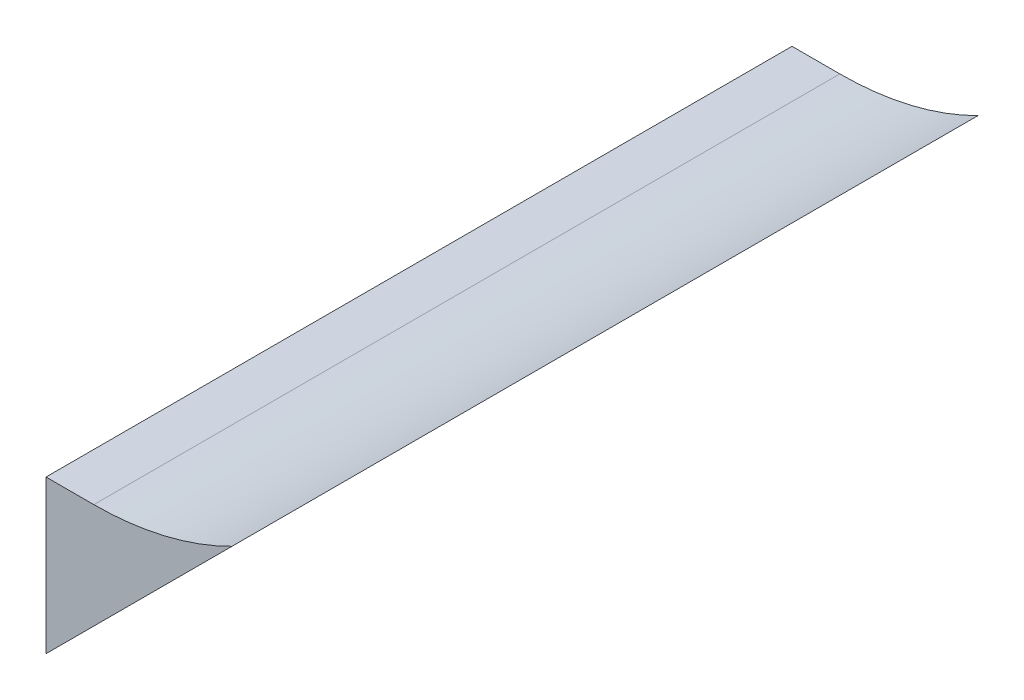
SolidWorks part; units mm, degrees
ref_plane "Спереди" through (0, 0, 0) normal (0, 0, 1) x (1, 0, 0)
ref_plane "Сверху" through (0, 0, 0) normal (0, 1, 0) x (1, 0, 0)
ref_plane "Слева" through (0, 0, 0) normal (1, 0, 0) x (0, 0, -1)
sketch "Эскиз1" plane through (0, 0, 0) normal (0, 0, 1) x (1, 0, 0)
  line L0 (-323.5, 0) -> (-323.5, -8) construction
  line L1 (-323.5, 0) -> (-323.5, -8)
  line L2 (-323.5, 0) -> (-321, 0)
  line L3 (-323.5, 0) -> (-315.5, 0) construction
  line L4 (-323.5, -8) -> (-315.5, 0)
  line L5 (-315.5, 0) -> (-313.7767, 1.7233)
  arc A0 (-321, 0) -> (-309.6863, 4.6863) centre (-321, 16) ccw construction
  arc A1 (-321, 0) -> (-313.7767, 1.7233) centre (-321, 16) ccw
extrude "Вытянуть1" add sketch "Эскиз1" against normal blind 39
